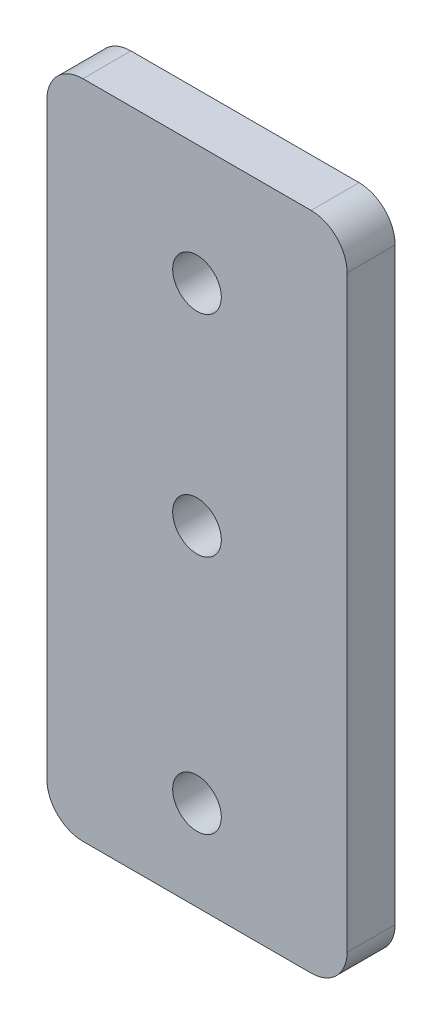
SolidWorks part; units mm, degrees
material "Thornel Mat VMA"
ref_plane "前视基准面" through (0, 0, 0) normal (0, 0, 1) x (1, 0, 0)
ref_plane "上视基准面" through (0, 0, 0) normal (0, 1, 0) x (1, 0, 0)
ref_plane "右视基准面" through (0, 0, 0) normal (1, 0, 0) x (0, 0, -1)
other "Configuration Table"
sketch "草图1" plane through (0, 0, 0) normal (0, 0, 1) x (1, 0, 0)
  line L1 (-12.5, -27.5) -> (12.5, -27.5)
  line L2 (-12.5, -27.5) -> (-12.5, 27.5)
  line L3 (-12.5, 27.5) -> (12.5, 27.5)
  line L4 (12.5, -27.5) -> (12.5, 27.5)
  line L5 (-12.5, -27.5) -> (12.5, 27.5) construction
  line L6 (-12.5, 27.5) -> (12.5, -27.5) construction
  point P0 (0, 0)
  dimension "D1" = 55
  dimension "D2" = 25
extrude "凸台-拉伸1" add sketch "草图1" along normal mid plane 4
sketch "草图2" plane through (0, 0, 2) normal (0, 0, 1) x (1, 0, 0)
  line L0 (12.5, 27.5) -> (-12.5, 27.5) construction
  line L1 (12.5, -27.5) -> (12.5, 27.5) construction
  circle A11 centre (0, 17.5) radius 2.025
  circle A15 centre (0, 0) radius 2.025
  circle A16 centre (0, -20) radius 2.025
  dimension "D1" = 4.05
  dimension "D2" = 10
  dimension "D3" = 20
  dimension "D4" = 12.5
extrude "切除-拉伸1" cut sketch "草图2" against normal mid plane 24
fillet "圆角1" radius 3 4 edges at (12.5, -27.5, 0) (-12.5, -27.5, 0) (12.5, 27.5, 0) (-12.5, 27.5, 0)
